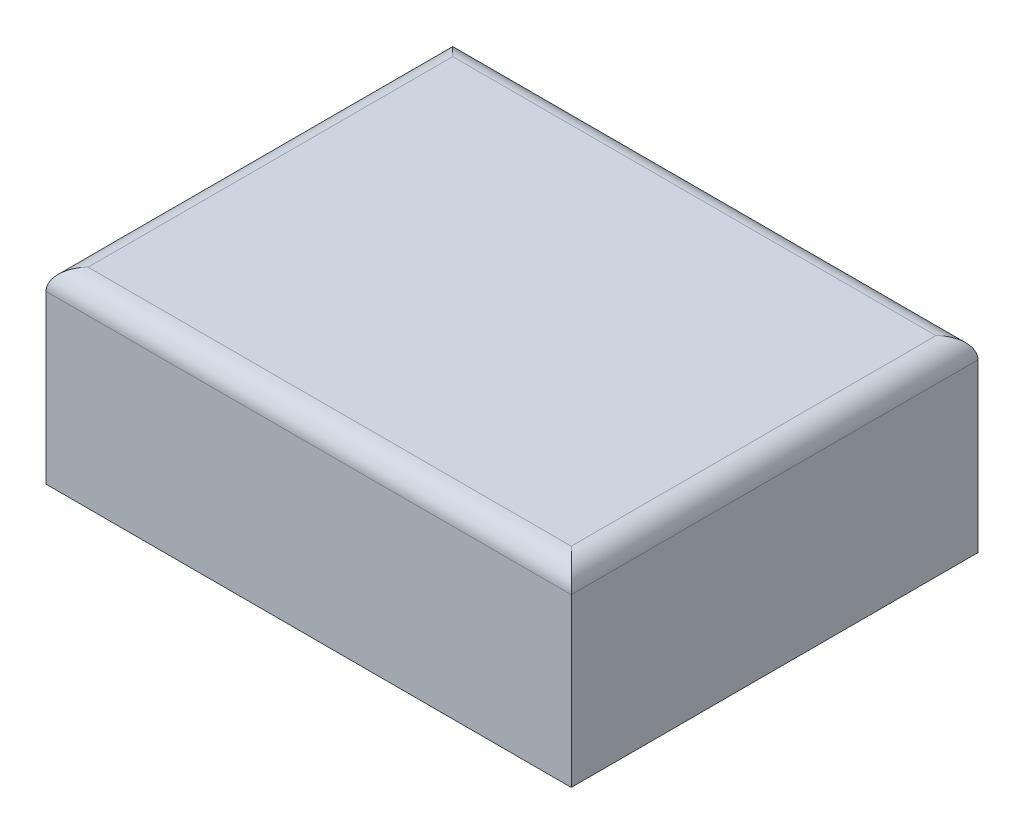
SolidWorks part; units mm, degrees
ref_plane "Front Plane" through (0, 0, 0) normal (0, 0, 1) x (1, 0, 0)
ref_plane "Top Plane" through (0, 0, 0) normal (0, 1, 0) x (1, 0, 0)
ref_plane "Right Plane" through (0, 0, 0) normal (1, 0, 0) x (0, 0, -1)
ref_plane "Plane1" through (-262.9045, -71.9862, 442.0704) normal (1, 0, 0) x (0, 0, -1)
sketch "Sketch2" plane through (-265.4045, 0, 0) normal (-1, 0, 0) x (0, 0, 1)
  line L1 (-96.7915, -44.7242) -> (96.7915, -44.7242)
  line L2 (-96.7915, -44.7242) -> (-96.7915, 44.7242)
  line L3 (-96.7915, 44.7242) -> (96.7915, 44.7242)
  line L4 (96.7915, -44.7242) -> (96.7915, 44.7242)
  line L5 (-96.7915, -44.7242) -> (96.7915, 44.7242) construction
  line L6 (-96.7915, 44.7242) -> (96.7915, -44.7242) construction
  point P0 (0, 0)
extrude "Boss-Extrude1" add sketch "Sketch2" along normal blind 250
fillet "Fillet1" radius 10 4 edges at (-390.4045, 44.7242, 96.7915) (-515.4045, 44.7242, 0) (-390.4045, 44.7242, -96.7915) (-265.4045, 44.7242, 0)
